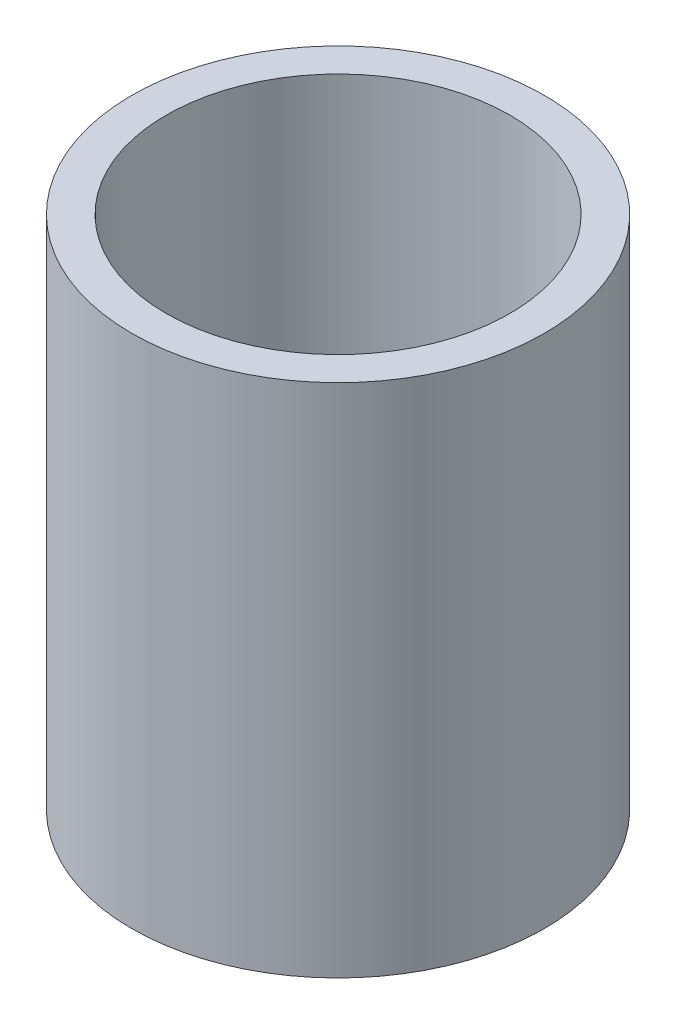
SolidWorks part; units mm, degrees
ref_plane "Front Plane" through (0, 0, 0) normal (0, 0, 1) x (1, 0, 0)
ref_plane "Top Plane" through (0, 0, 0) normal (0, 1, 0) x (1, 0, 0)
ref_plane "Right Plane" through (0, 0, 0) normal (1, 0, 0) x (0, 0, -1)
sketch "Sketch2" plane through (0, 0, 0) normal (0, 1, 0) x (1, 0, 0)
  circle A1 centre (0, 0) radius 60
  circle A2 centre (0, 0) radius 50
  dimension "D1" = 100
  dimension "D2" = 120
extrude "Boss-Extrude1" add sketch "Sketch2" along normal blind 150
